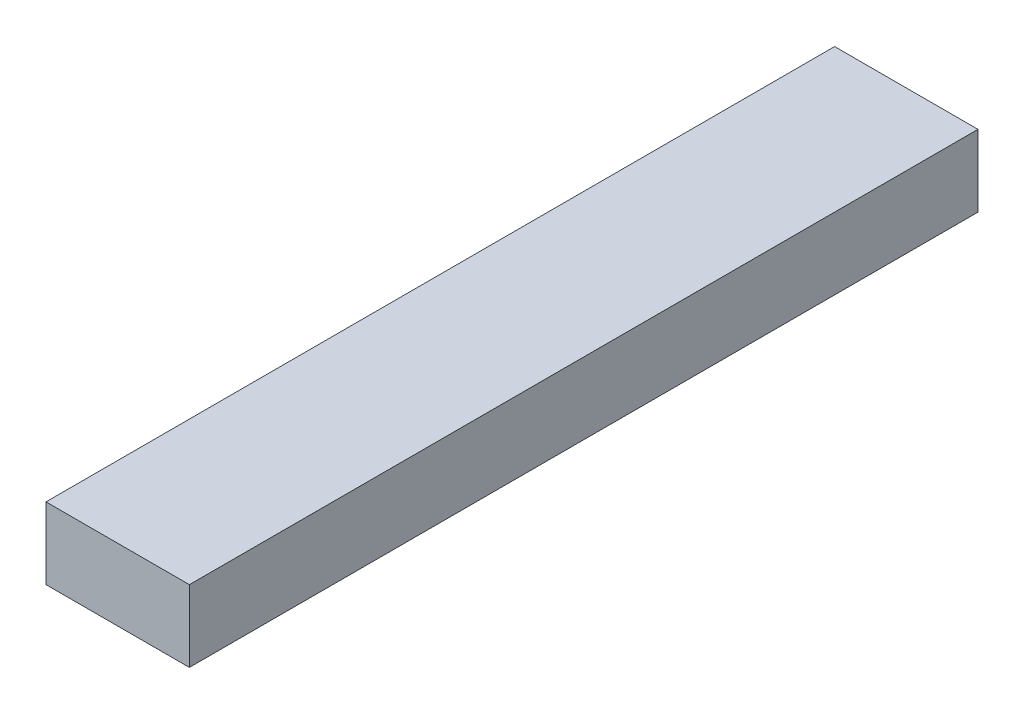
SolidWorks part; units mm, degrees
ref_plane "Front Plane" through (0, 0, 0) normal (0, 0, 1) x (1, 0, 0)
ref_plane "Top Plane" through (0, 0, 0) normal (0, 1, 0) x (1, 0, 0)
ref_plane "Right Plane" through (0, 0, 0) normal (1, 0, 0) x (0, 0, -1)
sketch "Sketch1" plane through (0, 0, 0) normal (0, 1, 0) x (1, 0, 0)
  line L0 (-10, 55) -> (10, -55) construction
  line L1 (-10, 55) -> (10, 55)
  line L2 (-10, 55) -> (-10, -55)
  line L3 (-10, -55) -> (10, -55)
  line L4 (10, 55) -> (10, -55)
  dimension "D1" = 20
  dimension "D2" = 110
extrude "Boss-Extrude1" add sketch "Sketch1" along normal blind 10
